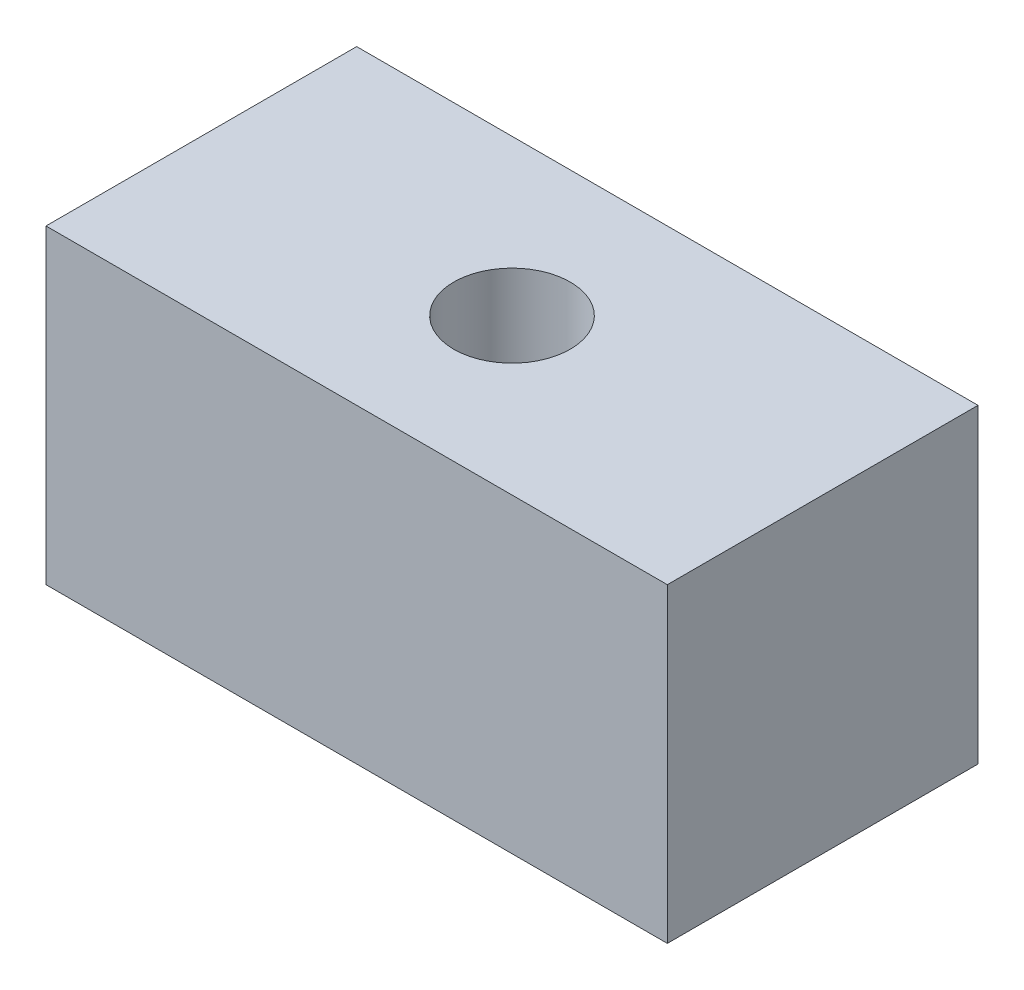
SolidWorks part; units mm, degrees
ref_plane "Front Plane" through (0, 0, 0) normal (0, 0, 1) x (1, 0, 0)
ref_plane "Top Plane" through (0, 0, 0) normal (0, 1, 0) x (1, 0, 0)
ref_plane "Right Plane" through (0, 0, 0) normal (1, 0, 0) x (0, 0, -1)
sketch "Sketch1" plane through (0, 0, 0) normal (0, 0, 1) x (1, 0, 0)
  line L0 (0, 25.4) -> (0, -25.4)
  line L1 (-76.2, 0) -> (76.2, 0) construction
  point P6 (0, 0)
  dimension "Width" = 152.4
  dimension "Thk" = 50.8
sketch "Sketch2" plane through (0, 0, 0) normal (1, 0, 0) x (0, 0, -1)
  line L0 (76.2, 0) -> (-76.2, 0)
  point P4 (0, 0)
  dimension "Length" = 152.4
sketch "Sketch3" plane through (0, 0, 0) normal (0, 0, 1) x (1, 0, 0)
  line L5 (0, 0) -> (101.6, 0)
  line L6 (0, 0) -> (0, 50.8)
  line L7 (0, 50.8) -> (101.6, 50.8)
  line L8 (101.6, 0) -> (101.6, 50.8)
  point P0 (0, 0)
  dimension "D1" = 101.6
  dimension "D2" = 50.8
extrude "Boss-Extrude1" add sketch "Sketch3" along normal blind 50.8
sketch "Sketch4" plane through (0, 50.8, 0) normal (0, 1, 0) x (1, 0, 0)
  line L0 (0, -25.4) -> (101.6, -25.4) construction
  line L1 (0, -50.8) -> (0, 0) construction
  line L2 (101.6, -50.8) -> (101.6, 0) construction
  line L3 (50.8, 0) -> (50.8, -50.8) construction
  line L4 (101.6, 0) -> (0, 0) construction
  line L5 (101.6, -50.8) -> (0, -50.8) construction
  circle A0 centre (50.8, -25.4) radius 9.525
  dimension "D1" = 19.05
extrude "Cut-Extrude1" cut sketch "Sketch4" against normal through all
